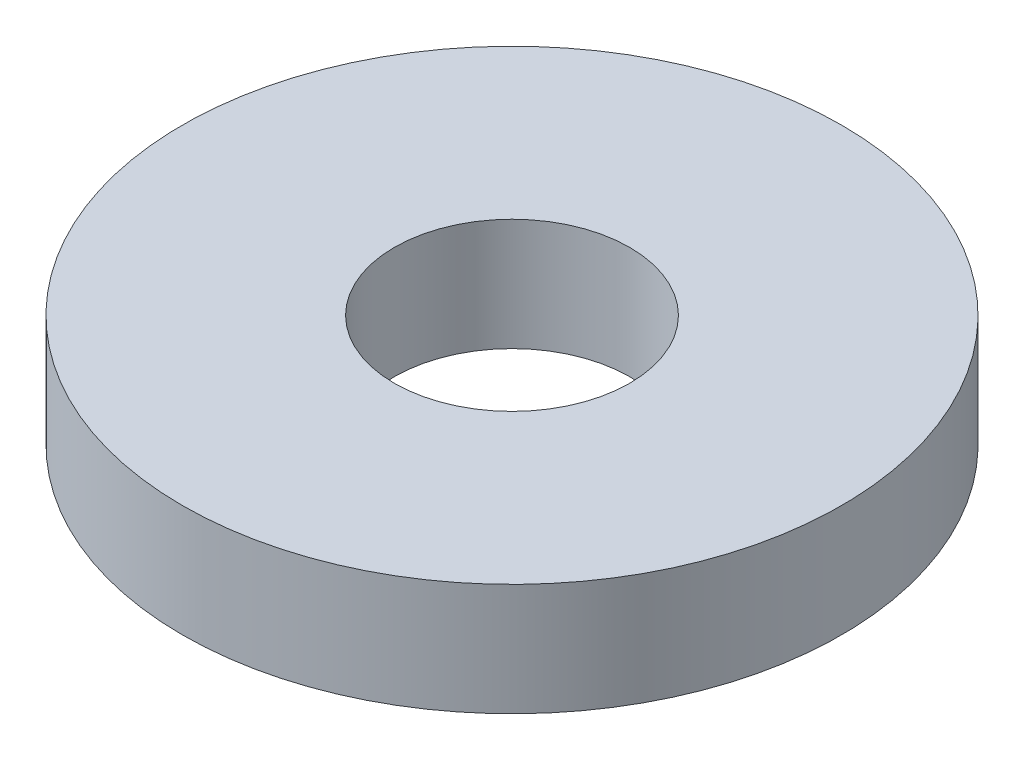
SolidWorks part; units mm, degrees
ref_plane "Front Plane" through (0, 0, 0) normal (0, 0, 1) x (1, 0, 0)
ref_plane "Top Plane" through (0, 0, 0) normal (0, 1, 0) x (1, 0, 0)
ref_plane "Right Plane" through (0, 0, 0) normal (1, 0, 0) x (0, 0, -1)
sketch "Sketch1" plane through (0, 0, 0) normal (0, 1, 0) x (1, 0, 0)
  circle A0 centre (0, 0) radius 12.5
  circle A1 centre (0, 0) radius 35
  dimension "D1" = 25
  dimension "D2" = 70
extrude "Boss-Extrude1" add sketch "Sketch1" along normal blind 11.9
